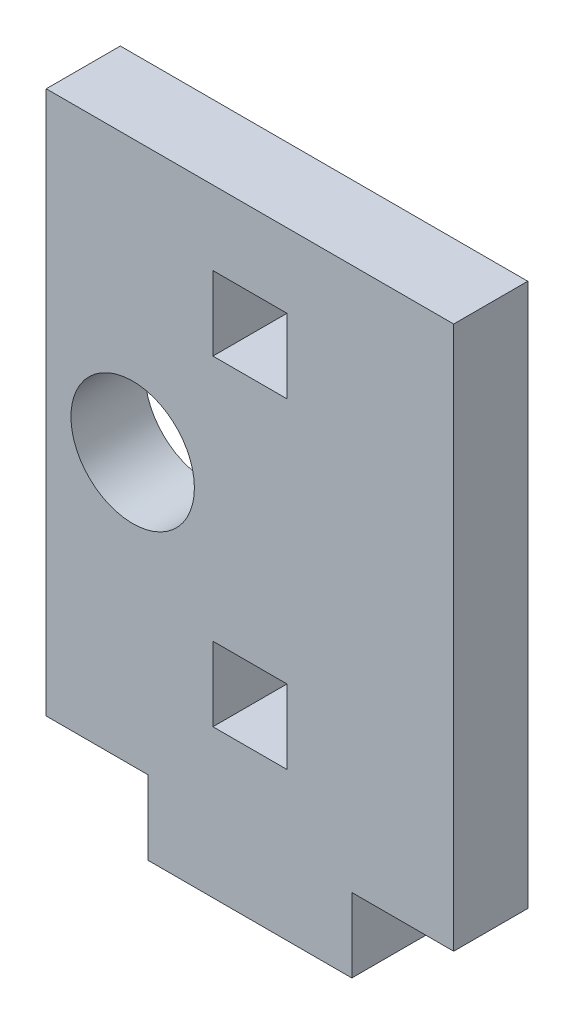
SolidWorks part; units mm, degrees
ref_plane "Front Plane" through (0, 0, 0) normal (0, 0, 1) x (1, 0, 0)
ref_plane "Top Plane" through (0, 0, 0) normal (0, 1, 0) x (1, 0, 0)
ref_plane "Right Plane" through (0, 0, 0) normal (1, 0, 0) x (0, 0, -1)
sketch "Sketch1" plane through (0, 0, 0) normal (0, 0, 1) x (1, 0, 0)
  line L1 (-8.25, 11) -> (8.25, 11)
  line L2 (-8.25, 11) -> (-8.25, -11)
  line L3 (-8.25, -11) -> (8.25, -11)
  line L4 (8.25, 11) -> (8.25, -11)
  point P0 (0, 0)
  dimension "D1" = 16.5
  dimension "D2" = 22
extrude "Boss-Extrude1" add sketch "Sketch1" along normal blind 3
sketch "Sketch2" plane through (0, -11, 0) normal (0, -1, 0) x (-1, 0, 0)
  line L0 (8.25, -3) -> (-8.25, -3) construction
  line L1 (4.125, -3) -> (-4.125, -3)
  line L2 (4.125, -3) -> (4.125, 0)
  line L3 (4.125, 0) -> (-4.125, 0)
  line L4 (-4.125, -3) -> (-4.125, 0)
  line L5 (8.25, 0) -> (-8.25, 0) construction
  line L6 (8.25, -3) -> (8.25, 0) construction
  dimension "D1" = 8.25
  dimension "D2" = 4.125
extrude "Boss-Extrude2" add sketch "Sketch2" along normal blind 3
sketch "Sketch3" plane through (0, 0, 3) normal (0, 0, 1) x (1, 0, 0)
  line L0 (-8.25, -11) -> (-4.125, -11) construction
  line L1 (-1.5, 8) -> (1.5, 8)
  line L2 (-1.5, 8) -> (-1.5, 5)
  line L3 (-1.5, 5) -> (1.5, 5)
  line L4 (1.5, 8) -> (1.5, 5)
  line L5 (8.25, 11) -> (-8.25, 11) construction
  line L6 (8.25, -11) -> (8.25, 11) construction
  line L7 (-1.5, -5) -> (1.5, -5)
  line L8 (-1.5, -5) -> (-1.5, -8)
  line L9 (-1.5, -8) -> (1.5, -8)
  line L10 (1.5, -5) -> (1.5, -8)
  point P0 (0, 0)
  point P6 (0.1219, -4.8607)
  dimension "D1" = 3
  dimension "D2" = 3
  dimension "D3" = 3
  dimension "D4" = 3
  dimension "D5" = 6.75
  dimension "D6" = 3
  dimension "D7" = 3
extrude "Cut-Extrude1" cut sketch "Sketch3" against normal blind 3
sketch "Sketch4" plane through (0, 0, 3) normal (0, 0, 1) x (1, 0, 0)
  line L0 (-8.25, 11) -> (-8.25, -11) construction
  circle A0 centre (-4.75, 0) radius 2.5
  dimension "D1" = 5
  dimension "D2" = 3.5
extrude "Cut-Extrude2" cut sketch "Sketch4" against normal blind 3
